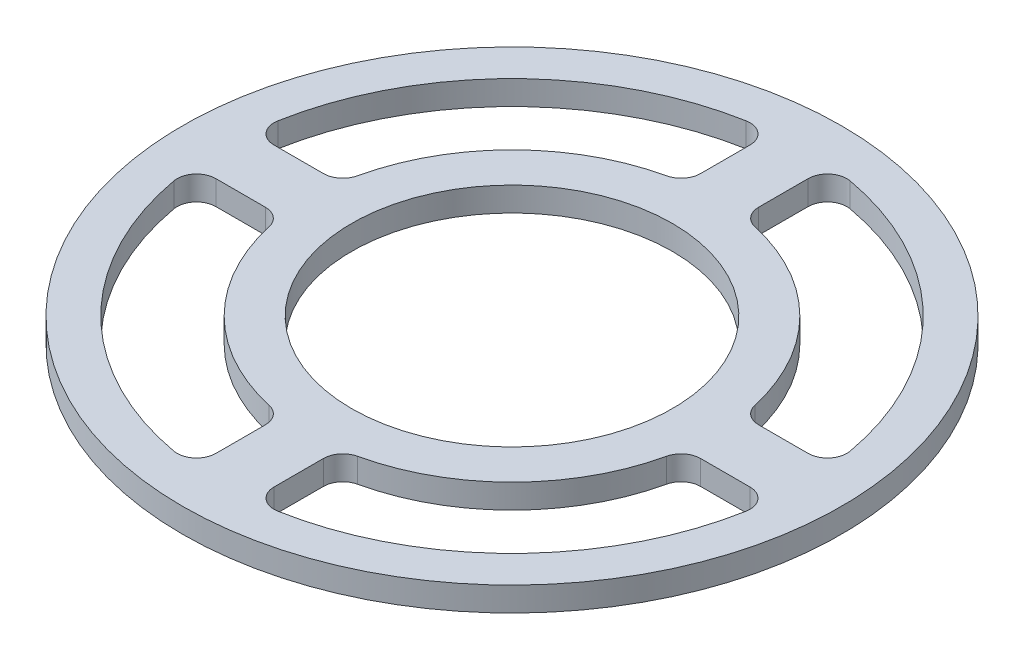
SolidWorks part; units mm, degrees
ref_plane "前视基准面" through (0, 0, 0) normal (0, 0, 1) x (1, 0, 0)
ref_plane "上视基准面" through (0, 0, 0) normal (0, 1, 0) x (1, 0, 0)
ref_plane "右视基准面" through (0, 0, 0) normal (1, 0, 0) x (0, 0, -1)
ref_plane "基准面4" through (0, 2.5, 0) normal (0, 1, 0) x (1, 0, 0)
sketch "草图1" plane through (0, 2.5, 0) normal (0, 1, 0) x (1, 0, 0)
  line L0 (-3, -22.4499) -> (-3, -27.55)
  line L1 (-27.55, -3) -> (-22.4499, -3)
  line L2 (-22.4499, 3) -> (-27.55, 3)
  line L3 (-3, 27.55) -> (-3, 22.4499)
  line L4 (3, 22.4499) -> (3, 27.55)
  line L5 (27.55, 3) -> (22.4499, 3)
  line L6 (22.4499, -3) -> (27.55, -3)
  line L7 (3, -27.55) -> (3, -22.4499)
  arc A0 (-22.4499, -3) -> (-20.4978, -4.5652) centre (-22.4499, -5) cw
  arc A1 (-20.4978, -4.5652) -> (-4.5652, -20.4978) centre (0, 0) ccw
  arc A2 (-4.5652, -20.4978) -> (-3, -22.4499) centre (-5, -22.4499) cw
  arc A3 (-3, -27.55) -> (-5.3571, -29.5178) centre (-5, -27.55) cw
  arc A4 (-5.3571, -29.5178) -> (-29.5178, -5.3571) centre (0, 0) cw
  arc A5 (-29.5178, -5.3571) -> (-27.55, -3) centre (-27.55, -5) cw
  arc A6 (-3, 22.4499) -> (-4.5652, 20.4978) centre (-5, 22.4499) cw
  arc A7 (-4.5652, 20.4978) -> (-20.4978, 4.5652) centre (0, 0) ccw
  arc A8 (-20.4978, 4.5652) -> (-22.4499, 3) centre (-22.4499, 5) cw
  arc A9 (-27.55, 3) -> (-29.5178, 5.3571) centre (-27.55, 5) cw
  arc A10 (-29.5178, 5.3571) -> (-5.3571, 29.5178) centre (0, 0) cw
  arc A11 (-5.3571, 29.5178) -> (-3, 27.55) centre (-5, 27.55) cw
  arc A12 (22.4499, 3) -> (20.4978, 4.5652) centre (22.4499, 5) cw
  arc A13 (20.4978, 4.5652) -> (4.5652, 20.4978) centre (0, 0) ccw
  arc A14 (4.5652, 20.4978) -> (3, 22.4499) centre (5, 22.4499) cw
  arc A15 (3, 27.55) -> (5.3571, 29.5178) centre (5, 27.55) cw
  arc A16 (5.3571, 29.5178) -> (29.5178, 5.3571) centre (0, 0) cw
  arc A17 (29.5178, 5.3571) -> (27.55, 3) centre (27.55, 5) cw
  arc A18 (3, -22.4499) -> (4.5652, -20.4978) centre (5, -22.4499) cw
  arc A19 (4.5652, -20.4978) -> (20.4978, -4.5652) centre (0, 0) ccw
  arc A20 (20.4978, -4.5652) -> (22.4499, -3) centre (22.4499, -5) cw
  arc A21 (27.55, -3) -> (29.5178, -5.3571) centre (27.55, -5) cw
  arc A22 (29.5178, -5.3571) -> (5.3571, -29.5178) centre (0, 0) cw
  arc A23 (5.3571, -29.5178) -> (3, -27.55) centre (5, -27.55) cw
  circle A24 centre (0, 0) radius 16.55
  circle A25 centre (0, 0) radius 34
extrude "凸台-拉伸1" add sketch "草图1" against normal blind 2.5
